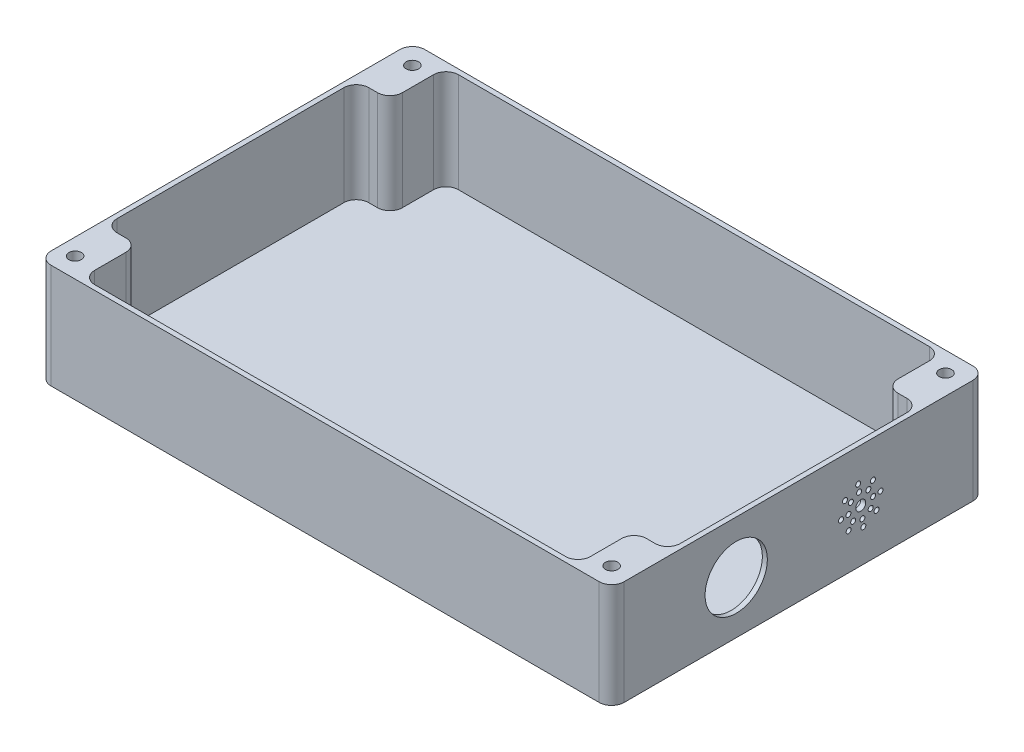
SolidWorks part; units mm, degrees
ref_plane "前视基准面" through (0, 0, 0) normal (0, 0, 1) x (1, 0, 0)
ref_plane "上视基准面" through (0, 0, 0) normal (0, 1, 0) x (1, 0, 0)
ref_plane "右视基准面" through (0, 0, 0) normal (1, 0, 0) x (0, 0, -1)
sketch "草图1" plane through (0, 0, 0) normal (0, 1, 0) x (1, 0, 0)
  line L1 (0, 0) -> (230, 0)
  line L2 (0, 0) -> (0, 150)
  line L3 (0, 150) -> (230, 150)
  line L4 (230, 0) -> (230, 150)
  dimension "D1" = 150
  dimension "D2" = 230
extrude "凸台-拉伸1" add sketch "草图1" along normal blind 42 contours L2 L1 L4 L3
sketch "草图4" plane through (0, 42, 0) normal (0, 1, 0) x (1, 0, 0)
  line L0 (0, 0) -> (0, 150) construction
  line L1 (0, 127.5) -> (13.5, 127.5)
  line L2 (0, 127.5) -> (0, 22.5)
  line L3 (0, 22.5) -> (13.5, 22.5)
  line L4 (230, 127.5) -> (230, 22.5)
  line L5 (230, 0) -> (230, 150) construction
  line L6 (0, 150) -> (230, 150) construction
  line L7 (13.5, 150) -> (216.5, 150)
  line L8 (13.5, 150) -> (13.5, 127.5)
  line L9 (13.5, 0) -> (216.5, 0)
  line L10 (216.5, 150) -> (216.5, 127.5)
  line L11 (0, 0) -> (230, 0) construction
  line L12 (216.5, 127.5) -> (230, 127.5)
  line L13 (13.5, 22.5) -> (13.5, 0)
  line L14 (216.5, 22.5) -> (216.5, 0)
  line L15 (216.5, 22.5) -> (230, 22.5)
  line L16 (2, 125.5) -> (2, 24.5)
  line L17 (2, 24.5) -> (15.5, 24.5)
  line L18 (15.5, 24.5) -> (15.5, 2)
  line L19 (15.5, 2) -> (214.5, 2)
  line L20 (214.5, 24.5) -> (214.5, 2)
  line L21 (214.5, 24.5) -> (228, 24.5)
  line L22 (228, 125.5) -> (228, 24.5)
  line L23 (214.5, 125.5) -> (228, 125.5)
  line L24 (214.5, 148) -> (214.5, 125.5)
  line L25 (15.5, 148) -> (214.5, 148)
  line L26 (15.5, 148) -> (15.5, 125.5)
  line L27 (2, 125.5) -> (15.5, 125.5)
  point P16 (115, 150)
  point P17 (0, 75)
  dimension "D1" = 203
  dimension "D2" = 105
  dimension "D3" = 2
extrude "切除-拉伸2" cut sketch "草图4" against normal blind 40 contours L16 L17 L18 L19 L20 L21 L22 L23 L24 L25 L26 L27
fillet "圆角1" radius 5 4 edges at (0, 21, 0) (0, 21, -150) (230, 21, -150) (230, 21, 0)
fillet "圆角2" radius 5 12 edges at (228, 22, -125.5) (214.5, 22, -125.5) (214.5, 22, -148) (15.5, 22, -148) (15.5, 22, -125.5) (2, 22, -125.5) (2, 22, -24.5) (15.5, 22, -24.5) (15.5, 22, -2) (228, 22, -24.5) (214.5, 22, -2) (214.5, 22, -24.5)
sketch "草图5" plane through (0, 42, 0) normal (0, 1, 0) x (1, 0, 0)
  line L0 (5, 0) -> (225, 0) construction
  line L1 (230, 5) -> (230, 145) construction
  line L2 (0, 5) -> (0, 145) construction
  line L3 (5, 150) -> (225, 150) construction
  circle A0 centre (222, 142) radius 2.5
  circle A1 centre (6.6318, 8) radius 2.5
  circle A3 centre (222, 8) radius 2.5
  circle A4 centre (8, 142) radius 2.5
  dimension "D1" = 8
  dimension "D2" = 8
  dimension "D3" = 8
  dimension "D4" = 8
extrude "切除-拉伸3" cut sketch "草图5" against normal through all
sketch "草图6" plane through (230, 0, 0) normal (1, 0, 0) x (0, 0, -1)
  line L0 (5, 42) -> (5, 0) construction
  line L1 (0, 0) -> (0, 42) construction
  circle A0 centre (50, 21) radius 12.5
  point P2 (0, 0)
  point P5 (5, 21)
  point P6 (0, 0)
  dimension "D1" = 50
extrude "切除-拉伸4" cut sketch "草图6" against normal blind 10 contours A0
sketch "草图9" plane through (230, 0, 0) normal (1, 0, 0) x (0, 0, -1)
  line L0 (150, 42) -> (150, 0) construction
  line L1 (145, 0) -> (145, 42) construction
  line L2 (100, 21) -> (103.0436, 24.9669) construction
  line L3 (103.0436, 24.9669) -> (108.3305, 31.8575) construction
  circle A0 centre (100, 21) radius 2
  circle A1 centre (103.0436, 24.9669) radius 1
  circle A2 centre (104.8698, 27.347) radius 1
  circle A3 centre (104.9572, 21.6528) radius 1
  circle A4 centre (103.9669, 17.9564) radius 1
  circle A5 centre (100.6528, 16.0428) radius 1
  circle A6 centre (96.9564, 17.0331) radius 1
  circle A7 centre (95.0428, 20.3472) radius 1
  circle A8 centre (96.0331, 24.0436) radius 1
  circle A9 centre (99.3472, 25.9572) radius 1
  circle A10 centre (107.9315, 22.0445) radius 1
  circle A11 centre (106.347, 16.1302) radius 1
  circle A12 centre (101.0445, 13.0685) radius 1
  circle A13 centre (95.1302, 14.653) radius 1
  circle A14 centre (92.0685, 19.9555) radius 1
  circle A15 centre (93.653, 25.8698) radius 1
  circle A16 centre (98.9555, 28.9315) radius 1
  point P7 (145, 21)
  dimension "D1" = 50
  dimension "D2" = 5
  dimension "D3" = 8
  dimension "D4" = 8
  dimension "D5" = 8
extrude "切除-拉伸5" cut sketch "草图9" against normal up to next
